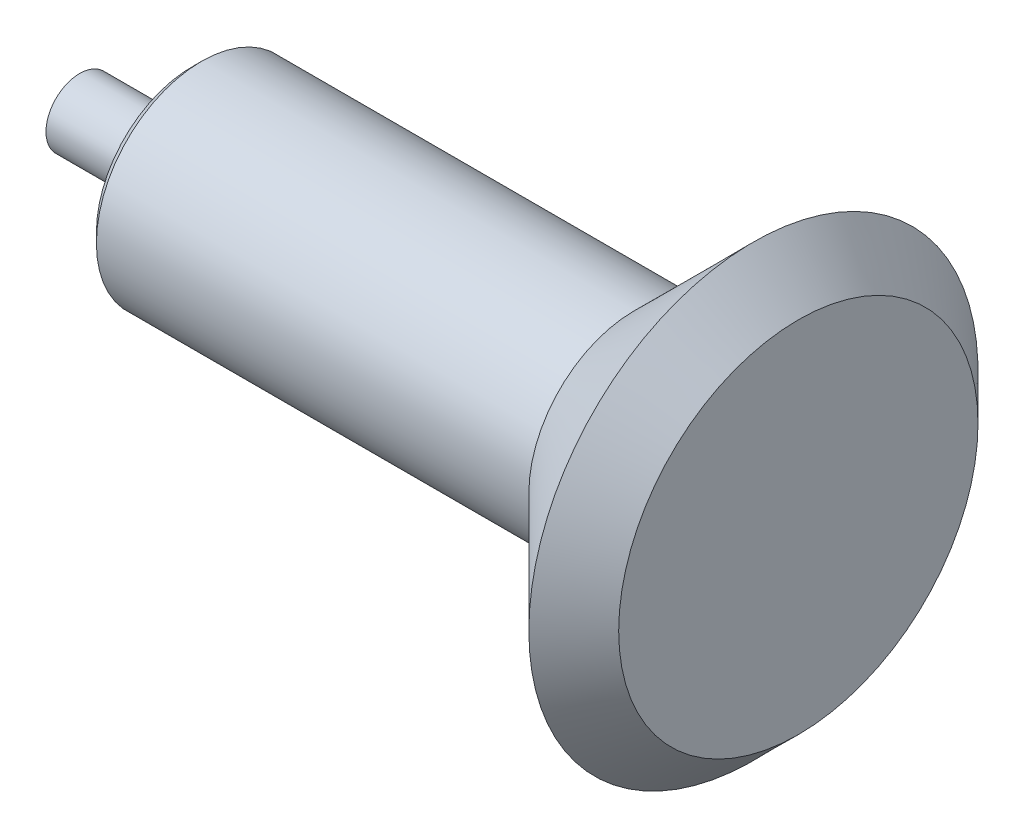
SolidWorks part; units mm, degrees
ref_plane "Ön Düzlem" through (0, 0, 0) normal (0, 0, 1) x (1, 0, 0)
ref_plane "Üst Düzlem" through (0, 0, 0) normal (0, 1, 0) x (1, 0, 0)
ref_plane "Sağ Düzlem" through (0, 0, 0) normal (1, 0, 0) x (0, 0, -1)
sketch "Çizim1" plane through (0, 0, 0) normal (0, 0, 1) x (1, 0, 0)
  line L0 (0, 0) -> (160, 0) construction
  line L1 (0, -7.5) -> (0, 7.5)
  line L2 (0, 7.5) -> (25, 7.5)
  line L3 (25, 7.5) -> (25, 21.2814)
  line L4 (25, 21.2814) -> (27.1213, 23.4027)
  line L5 (27.1213, 23.4027) -> (123.4027, 23.4027)
  line L6 (160, -40) -> (150, -50)
  line L7 (160, -40) -> (160, 40)
  line L9 (160, 40) -> (150, 50)
  line L10 (123.4027, -23.4027) -> (150, -50)
  line L11 (27.1213, -23.4027) -> (123.4027, -23.4027)
  line L12 (123.4027, 23.4027) -> (150, 50)
  line L13 (25, -21.2814) -> (27.1213, -23.4027)
  line L14 (25, -7.5) -> (25, -21.2814)
  line L15 (160, -40) -> (150, -50)
  line L16 (0, -7.5) -> (25, -7.5)
  dimension "D1" = 160
  dimension "D2" = 7.5
  dimension "D3" = 25
  dimension "D4" = 135
  dimension "D5" = 23.4027
  dimension "D6" = 3
  dimension "D7" = 50
  dimension "D8" = 135
  dimension "D9" = 40
  dimension "D10" = 37.6143
  dimension "D11" = 135
revolve "Döndür3" add sketch "Çizim1" angle 360 about L0
